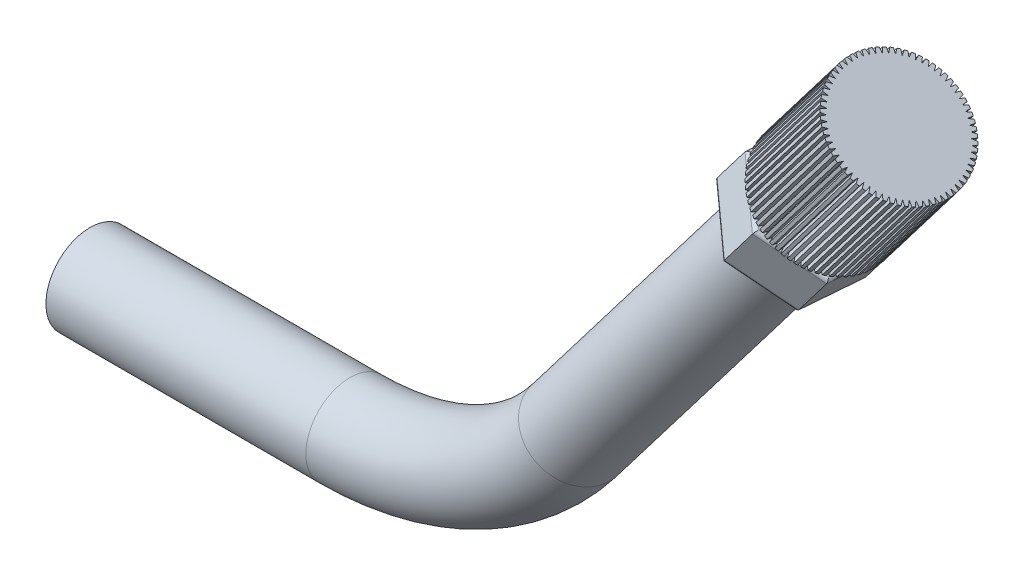
SolidWorks part; units mm, degrees
material "Cast Alloy Steel"
ref_plane "Front Plane" through (0, 0, 0) normal (0, 0, 1) x (1, 0, 0)
ref_plane "Top Plane" through (0, 0, 0) normal (0, 1, 0) x (1, 0, 0)
ref_plane "Right Plane" through (0, 0, 0) normal (1, 0, 0) x (0, 0, -1)
sketch "Sketch1" plane through (0, 0, 0) normal (0, 0, 1) x (1, 0, 0)
  line L0 (27.4548, 6.2987) -> (39.5931, 22.194)
  line L1 (14.7197, 0) -> (0, 0)
  arc A0 (14.7197, 0) -> (27.4548, 6.2987) centre (14.7197, 16.0237) ccw
  dimension "D2" = 20
sketch "Sketch2" plane through (0, 0, 0) normal (1, 0, 0) x (0, 0, -1)
  circle A0 centre (0, 0) radius 2.5
sweep "Sweep3" add profiles "Sketch2" path "Sketch1"
cosmetic thread "Cosmetic Thread1" parameters "D2"=4.11
sketch "Sketch3" plane through (25.2893, 33.1169, 0) normal (0.6069, 0.7948, 0) x (0.7948, -0.6069, 0)
  line L1 (18.2055, 3.6185) -> (14.9677, 1.9894)
  line L2 (14.9677, 1.9894) -> (14.7597, -1.6291)
  line L3 (14.7597, -1.6291) -> (17.7895, -3.6185)
  line L4 (17.7895, -3.6185) -> (21.0272, -1.9894)
  line L5 (21.0272, -1.9894) -> (21.2352, 1.6291)
  line L6 (21.2352, 1.6291) -> (18.2055, 3.6185)
  circle A0 centre (17.9975, 0) radius 3.1389 construction
extrude "Boss-Extrude1" add sketch "Sketch3" along normal blind 3
sketch "Sketch4" plane through (27.11, 35.5013, 0) normal (0.6069, 0.7948, 0) x (0.7948, -0.6069, 0)
  line L0 (18.2055, 3.6185) -> (17.7895, -3.6185) construction
  circle A0 centre (17.9975, 0) radius 1
extrude "Boss-Extrude3" add sketch "Sketch4" along normal blind 0.25
sketch "Sketch5" plane through (27.2618, 35.6999, 0) normal (0.6069, 0.7948, 0) x (0.7948, -0.6069, 0)
  circle A0 centre (17.9975, 0) radius 3.5
extrude "Boss-Extrude4" add sketch "Sketch5" along normal blind 7
sketch "Sketch6" plane through (31.5102, 41.2633, 0) normal (0.6069, 0.7948, 0) x (0.7948, -0.6069, 0)
  line L1 (17.9229, 3.2157) -> (17.9896, 3.5)
  line L2 (17.9229, 3.2157) -> (17.8382, 3.4964)
  circle A0 centre (17.9975, 0) radius 3.5 construction
  arc A1 (17.8382, 3.4964) -> (17.9896, 3.5) centre (17.9135, 3.516) cw
  dimension "D1" = 30
  dimension "D2" = 0.3003
extrude "Cut-Extrude1" cut sketch "Sketch6" against normal blind 7
pattern_circular "CirPattern1" count 68 over 360 about axis through (14.3038, -10.9229, 0) along (0.6069, 0.7948, 0) of "Cut-Extrude1"
fillet "Fillet2" radius 0.2 14 edges at (38.4718, 23.0503, -2.8039) (37.1025, 24.0959, -0.1801) (38.2238, 23.2397, 2.6238) (40.7144, 21.3378, 2.8039) (42.0837, 20.2921, 0.1801) (40.9624, 21.1484, -2.6238) (39.5931, 22.194, -2.5) (43.9044, 22.6764, 0.1801) (42.5352, 23.7221, 2.8039) (40.0446, 25.624, 2.6238) (38.9233, 26.4802, -0.1801) (40.2925, 25.4346, -2.8039) (42.7831, 23.5327, -2.6238) (40.6191, 25.1853, 0)
